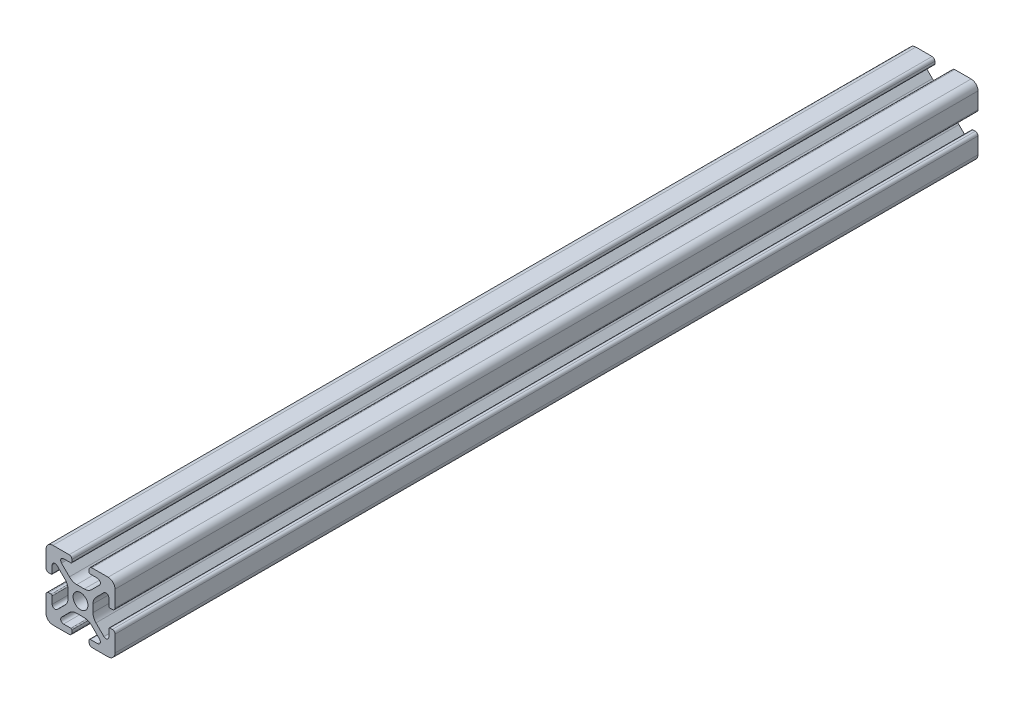
SolidWorks part; units mm, degrees
ref_plane "Front Plane" through (0, 0, 0) normal (0, 0, 1) x (1, 0, 0)
ref_plane "Top Plane" through (0, 0, 0) normal (0, 1, 0) x (1, 0, 0)
ref_plane "Right Plane" through (0, 0, 0) normal (1, 0, 0) x (0, 0, -1)
sketch "Sketch1" plane through (0, 0, 0) normal (0, 0, 1) x (1, 0, 0)
  line L0 (0, 10) -> (0, -10) construction
  line L1 (10, 0) -> (-10, 0) construction
  line L2 (-2.5, 10) -> (2.5, 10) construction
  line L3 (-5.75, 8.2) -> (5.75, 8.2) construction
  circle A0 centre (0, 0) radius 2.15 construction
  point P4 (0, 0)
  point P8 (0, 0)
  point P10 (0, 3.6)
  point P14 (0, 10)
  point P17 (0, 8.2)
  dimension "Thru Hole" = 4.3
  dimension "Height" = 20
  dimension "T Slot Depth" = 6.4
  dimension "T Slot Top Width" = 5
  dimension "T Slot Max Width" = 11.5
  dimension "Wall" = 1.8
sketch "Sketch2" plane through (0, 0, 0) normal (1, 0, 0) x (0, 0, -1)
  line L0 (125, 0) -> (-125, 0) construction
  point P4 (0, 0)
  dimension "D1" = 250
sketch "Sketch3" plane through (0, 0, 0) normal (0, 0, 1) x (1, 0, 0)
  line L0 (3.2874, 10) -> (8, 10)
  line L1 (10, 8) -> (10, -8) construction
  line L2 (8, -10) -> (-8, -10) construction
  line L3 (-10, 10) -> (10, -10) construction
  line L4 (2.5, 9.2126) -> (2.5, 8.5048)
  line L5 (-5.75, 8.2) -> (5.75, 8.2) construction
  line L6 (2.8048, 8.2) -> (4.9118, 8.2)
  line L7 (5.5045, 6.7691) -> (3.2141, 4.4787)
  line L8 (1.0928, 3.6) -> (-1.0928, 3.6)
  line L9 (0, 10) -> (0, -10) construction
  line L10 (5.75, 8.2) -> (5.75, 0) construction
  line L11 (10, 0) -> (-10, 0) construction
  line L12 (0, 0) -> (0, 10) construction
  line L13 (-2.5, 9.2126) -> (-2.5, 8.5048)
  line L14 (-5.5045, 6.7691) -> (-3.2141, 4.4787)
  line L15 (-2.8048, 8.2) -> (-4.9118, 8.2)
  line L16 (-3.2874, 10) -> (-8, 10)
  line L17 (0, 0) -> (-10, 0) construction
  line L18 (-10, 3.2874) -> (-10, 8)
  line L19 (-8.2, 2.8048) -> (-8.2, 4.9118)
  line L20 (-6.7691, 5.5045) -> (-4.4787, 3.2141)
  line L21 (-9.2126, 2.5) -> (-8.5048, 2.5)
  line L22 (-3.6, -1.0928) -> (-3.6, 1.0928)
  line L23 (-6.7691, -5.5045) -> (-4.4787, -3.2141)
  line L24 (-8.2, -2.8048) -> (-8.2, -4.9118)
  line L25 (-9.2126, -2.5) -> (-8.5048, -2.5)
  line L26 (-10, -3.2874) -> (-10, -8)
  line L27 (9.2126, -2.5) -> (8.5048, -2.5)
  line L28 (8.2, -2.8048) -> (8.2, -4.9118)
  line L29 (6.7691, -5.5045) -> (4.4787, -3.2141)
  line L30 (3.6, -1.0928) -> (3.6, 1.0928)
  line L31 (9.2126, 2.5) -> (8.5048, 2.5)
  line L32 (6.7691, 5.5045) -> (4.4787, 3.2141)
  line L33 (8.2, 2.8048) -> (8.2, 4.9118)
  line L34 (10, 8) -> (10, 3.2874)
  line L35 (10, -3.2874) -> (10, -8)
  line L36 (3.2874, -10) -> (8, -10)
  line L37 (-3.2874, -10) -> (-8, -10)
  line L38 (-6.7691, -5.5045) -> (-4.4787, -3.2141)
  line L39 (-2.8048, -8.2) -> (-4.9118, -8.2)
  line L40 (-5.5045, -6.7691) -> (-3.2141, -4.4787)
  line L41 (-2.5, -9.2126) -> (-2.5, -8.5048)
  line L42 (1.0928, -3.6) -> (-1.0928, -3.6)
  line L43 (5.5045, -6.7691) -> (3.2141, -4.4787)
  line L44 (2.8048, -8.2) -> (4.9118, -8.2)
  line L45 (2.5, -9.2126) -> (2.5, -8.5048)
  arc A0 (4.9118, 8.2) -> (5.5045, 6.7691) centre (4.9118, 7.3618) cw
  arc A1 (3.2141, 4.4787) -> (1.0928, 3.6) centre (1.0928, 6.6) cw
  circle A2 centre (0, 0) radius 2.15 construction
  circle A3 centre (0, 0) radius 2.15
  arc A4 (3.2874, 10) -> (2.5, 9.2126) centre (3.2874, 9.2126) ccw
  arc A5 (2.5, 8.5048) -> (2.8048, 8.2) centre (2.8048, 8.5048) ccw
  arc A6 (-3.2874, 10) -> (-2.5, 9.2126) centre (-3.2874, 9.2126) cw
  arc A7 (-4.9118, 8.2) -> (-5.5045, 6.7691) centre (-4.9118, 7.3618) ccw
  arc A8 (-3.2141, 4.4787) -> (-1.0928, 3.6) centre (-1.0928, 6.6) ccw
  arc A9 (-2.5, 8.5048) -> (-2.8048, 8.2) centre (-2.8048, 8.5048) cw
  arc A10 (-8.5048, 2.5) -> (-8.2, 2.8048) centre (-8.5048, 2.8048) ccw
  arc A11 (-4.4787, 3.2141) -> (-3.6, 1.0928) centre (-6.6, 1.0928) cw
  arc A12 (-8.2, 4.9118) -> (-6.7691, 5.5045) centre (-7.3618, 4.9118) cw
  arc A13 (-10, 3.2874) -> (-9.2126, 2.5) centre (-9.2126, 3.2874) ccw
  arc A14 (-8.5048, -2.5) -> (-8.2, -2.8048) centre (-8.5048, -2.8048) cw
  arc A15 (-10, -3.2874) -> (-9.2126, -2.5) centre (-9.2126, -3.2874) cw
  arc A16 (-4.4787, -3.2141) -> (-3.6, -1.0928) centre (-6.6, -1.0928) ccw
  arc A17 (-8.2, -4.9118) -> (-6.7691, -5.5045) centre (-7.3618, -4.9118) ccw
  arc A26 (-8, -10) -> (-10, -8) centre (-8, -8) cw
  arc A27 (-8, 10) -> (-10, 8) centre (-8, 8) ccw
  arc A28 (8, 10) -> (10, 8) centre (8, 8) cw
  arc A29 (10, -8) -> (8, -10) centre (8, -8) cw
  arc A30 (8.2, -4.9118) -> (6.7691, -5.5045) centre (7.3618, -4.9118) cw
  arc A31 (4.4787, -3.2141) -> (3.6, -1.0928) centre (6.6, -1.0928) cw
  arc A32 (10, -3.2874) -> (9.2126, -2.5) centre (9.2126, -3.2874) ccw
  arc A33 (8.5048, -2.5) -> (8.2, -2.8048) centre (8.5048, -2.8048) ccw
  arc A34 (10, 3.2874) -> (9.2126, 2.5) centre (9.2126, 3.2874) cw
  arc A35 (8.2, 4.9118) -> (6.7691, 5.5045) centre (7.3618, 4.9118) ccw
  arc A36 (4.4787, 3.2141) -> (3.6, 1.0928) centre (6.6, 1.0928) ccw
  arc A37 (8.5048, 2.5) -> (8.2, 2.8048) centre (8.5048, 2.8048) cw
  arc A38 (-2.5, -8.5048) -> (-2.8048, -8.2) centre (-2.8048, -8.5048) ccw
  arc A39 (-3.2141, -4.4787) -> (-1.0928, -3.6) centre (-1.0928, -6.6) cw
  arc A40 (-4.9118, -8.2) -> (-5.5045, -6.7691) centre (-4.9118, -7.3618) cw
  arc A41 (-3.2874, -10) -> (-2.5, -9.2126) centre (-3.2874, -9.2126) ccw
  arc A42 (2.5, -8.5048) -> (2.8048, -8.2) centre (2.8048, -8.5048) cw
  arc A43 (3.2874, -10) -> (2.5, -9.2126) centre (3.2874, -9.2126) cw
  arc A44 (3.2141, -4.4787) -> (1.0928, -3.6) centre (1.0928, -6.6) ccw
  arc A45 (4.9118, -8.2) -> (5.5045, -6.7691) centre (4.9118, -7.3618) ccw
  point P36 (2.5, 10)
  point P39 (2.5, 8.2)
  point P49 (0, 3.6)
  point P77 (-3.6, 0)
  point P78 (-8.2, -2.5)
  point P79 (-10, -2.5)
  point P104 (-10, -10)
  point P110 (10, 10)
  point P114 (10, -2.5)
  point P115 (8.2, -2.5)
  point P116 (3.6, 0)
  point P141 (0, -3.6)
  dimension "D1" = 3
  dimension "D2" = 0.8382
  dimension "D4" = 0.7874
  dimension "D5" = 0.3048
  dimension "D6" = 2
  dimension "D3" = 45
extrude "Boss-Extrude1" add sketch "Sketch3" along normal up to vertex (125 mm away) and the other way up to vertex (125 mm away) contours A45 L44 A42 L45 A43 L36 A29 L35 A32 L27 A33 L28 A30 L29 A31 L30 A36 L32 A35 L33 A37 L31 A34 L34 A28 L0 A4 L4 A5 L6 A0 L7 A1 L8 A8 L14 A7 L15 A9 L13 A6 L16 A27 L18 A13 L21 A10 L19 A12 L20 A11 up to point (0, 0, 125) other way up to point (0, 0, -125)
